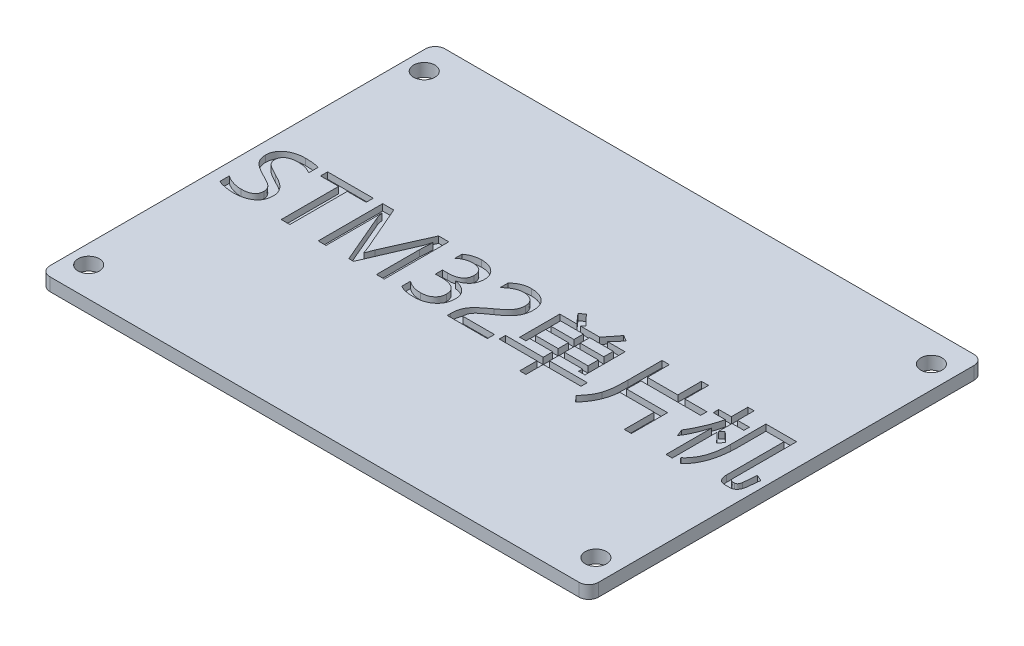
SolidWorks part; units mm, degrees
ref_plane "前视基准面" through (0, 0, 0) normal (0, 0, 1) x (1, 0, 0)
ref_plane "上视基准面" through (0, 0, 0) normal (0, 1, 0) x (1, 0, 0)
ref_plane "右视基准面" through (0, 0, 0) normal (1, 0, 0) x (0, 0, -1)
sketch "草图1" plane through (0, 0, 0) normal (0, 1, 0) x (1, 0, 0)
  line L0 (-55, 0) -> (55, 0) construction
  line L1 (41, -30.6) -> (-41, -30.6)
  line L2 (42.5, -29.1) -> (42.5, 29.1)
  line L3 (41, 30.6) -> (-41, 30.6)
  line L4 (-42.5, -29.1) -> (-42.5, 29.1)
  line L5 (42.5, -30.6) -> (-42.5, 30.6) construction
  line L6 (42.5, 30.6) -> (-42.5, -30.6) construction
  circle A0 centre (-39.6, 26) radius 1.65
  circle A1 centre (-39.6, -26) radius 1.65
  circle A4 centre (39, 26) radius 1.65
  circle A5 centre (39, -26) radius 1.65
  arc A6 (41, -30.6) -> (42.5, -29.1) centre (41, -29.1) ccw
  arc A7 (42.5, 29.1) -> (41, 30.6) centre (41, 29.1) ccw
  arc A8 (-41, -30.6) -> (-42.5, -29.1) centre (-41, -29.1) cw
  arc A9 (-41, 30.6) -> (-42.5, 29.1) centre (-41, 29.1) ccw
  point P0 (0, 0)
  dimension "D3" = 3.3
  dimension "D4" = 2.9
  dimension "D5" = 4.6
  dimension "D6" = 4.6
  dimension "D7" = 3.5
  dimension "D8" = 3.3
  dimension "D9" = 1.5
  dimension "D1" = 61.2
  dimension "D2" = 85
extrude "凸台-拉伸1" add sketch "草图1" along normal blind 2
sketch "草图2" plane through (0, 2, 0) normal (0, 1, 0) x (1, 0, 0)
  text T0 "STM32单片机" font "微软雅黑" height 10
  point P1 (-23.1786, -3.936)
  point P2 (-30.001, -3.4987)
  point P4 (-38.2228, -3.3237)
  point P5 (-39.9722, -4.1984)
  point P6 (0, 0)
  point P7 (0, 0)
  point P8 (0, 0)
  point P9 (-41.2842, -5.248)
  point P11 (0, 0)
  point P13 (-73.1219, 27.9018)
  dimension "D1" = 5
  dimension "D2" = 41.5
extrude "切除-拉伸1" cut sketch "草图2" against normal blind 1
